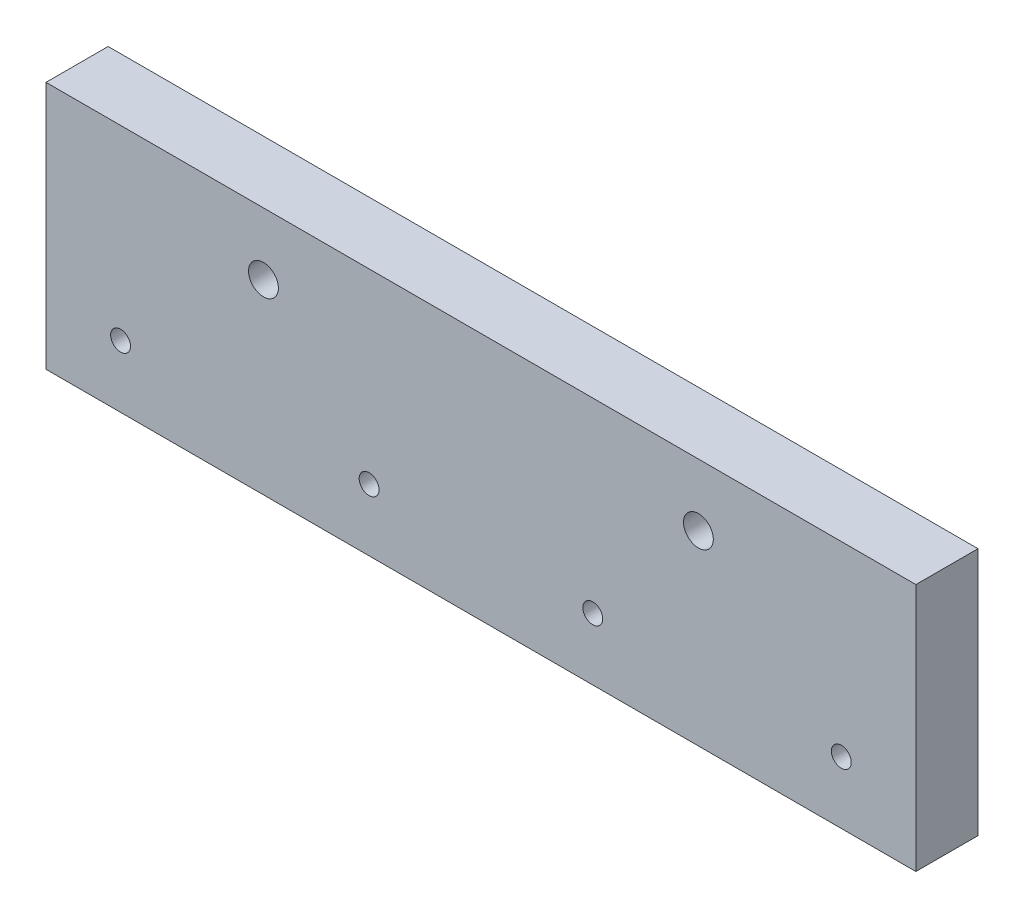
SolidWorks part; units mm, degrees
ref_plane "Front Plane" through (0, 0, 0) normal (0, 0, 1) x (1, 0, 0)
ref_plane "Top Plane" through (0, 0, 0) normal (0, 1, 0) x (1, 0, 0)
ref_plane "Right Plane" through (0, 0, 0) normal (1, 0, 0) x (0, 0, -1)
sketch "Sketch1" plane through (0, 0, 0) normal (0, 0, 1) x (1, 0, 0)
  line L1 (0, 0) -> (88.9, 0)
  line L2 (0, 0) -> (0, 25.4)
  line L3 (0, 25.4) -> (88.9, 25.4)
  line L4 (88.9, 0) -> (88.9, 25.4)
  dimension "D1" = 25.4
  dimension "D2" = 88.9
extrude "Boss-Extrude1" add sketch "Sketch1" along normal blind 6.35
sketch "Sketch2" plane through (0, 0, 6.35) normal (0, 0, 1) x (1, 0, 0)
  line L0 (0, 25.4) -> (0, 0) construction
  line L1 (44.45, 25.4) -> (44.45, 0) construction
  line L2 (88.9, 25.4) -> (0, 25.4) construction
  line L3 (0, 0) -> (88.9, 0) construction
  circle A0 centre (7.62, 6.35) radius 1.016
  circle A1 centre (33.02, 6.35) radius 1.016
  circle A2 centre (55.88, 6.35) radius 1.016
  circle A3 centre (81.28, 6.35) radius 1.016
  dimension "D1" = 2.032
  dimension "D2" = 2.032
  dimension "D3" = 25.4
  dimension "D4" = 7.62
  dimension "D5" = 6.35
extrude "Cut-Extrude1" cut sketch "Sketch2" against normal through all
sketch "Sketch3" plane through (0, 0, 6.35) normal (0, 0, 1) x (1, 0, 0)
  line L0 (0, 25.4) -> (0, 0) construction
  line L2 (88.9, 25.4) -> (0, 25.4) construction
  line L3 (44.45, 25.4) -> (44.45, 0) construction
  line L4 (0, 0) -> (88.9, 0) construction
  circle A0 centre (22.225, 19.05) radius 1.524
  circle A1 centre (66.675, 19.05) radius 1.524
  dimension "D3" = 3.048
  dimension "D1" = 22.225
  dimension "D2" = 6.35
extrude "Cut-Extrude2" cut sketch "Sketch3" against normal through all
